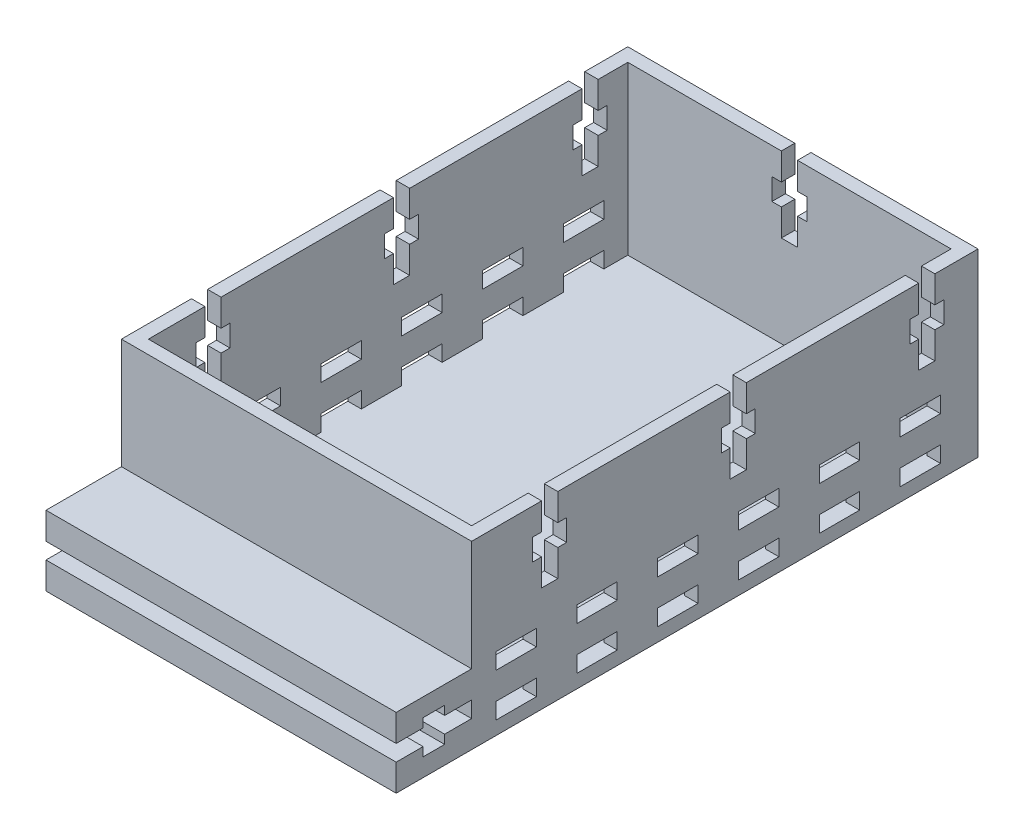
SolidWorks part; units mm, degrees
ref_plane "Front Plane" through (0, 0, 0) normal (0, 0, 1) x (1, 0, 0)
ref_plane "Top Plane" through (0, 0, 0) normal (0, 1, 0) x (1, 0, 0)
ref_plane "Right Plane" through (0, 0, 0) normal (1, 0, 0) x (0, 0, -1)
sketch "Sketch1" plane through (0, 0, 0) normal (0, 1, 0) x (1, 0, 0)
  line L1 (-30, 44.5) -> (30, 44.5)
  line L2 (-30, 44.5) -> (-30, -44.5)
  line L3 (-30, -44.5) -> (30, -44.5)
  line L4 (30, 44.5) -> (30, -44.5)
  point P4 (0, 44.5)
  point P6 (-30, 0)
  dimension "D1" = 89
  dimension "D2" = 60
extrude "Boss-Extrude1" add sketch "Sketch1" along normal blind 2.5
sketch "Sketch3" plane through (0, 0, 0) normal (0, 1, 0) x (1, 0, 0)
  line L0 (-30, 44.5) -> (-30, -44.5) construction
  line L1 (-32.5, 47) -> (32.5, 47)
  line L2 (-32.5, 47) -> (-32.5, -47)
  line L3 (-32.5, -47) -> (32.5, -47)
  line L4 (32.5, 47) -> (32.5, -47)
  line L5 (30, 44.5) -> (-30, 44.5) construction
  line L6 (30, -44.5) -> (30, 44.5) construction
  line L7 (-30, -44.5) -> (30, -44.5) construction
  line L9 (-30, 44.5) -> (30, 44.5)
  line L10 (-30, 44.5) -> (-30, -44.5)
  line L11 (-30, -44.5) -> (30, -44.5)
  line L12 (30, 44.5) -> (30, -44.5)
  dimension "D1" = 2.5
  dimension "D2" = 2.5
  dimension "D3" = 2.5
  dimension "D4" = 2.5
extrude "Boss-Extrude2" add sketch "Sketch3" along normal blind 33.5
sketch "Sketch5" plane through (0, 0, 0) normal (1, 0, 0) x (0, 0, -1)
  line L0 (-47, 0) -> (47, 0) construction
  line L1 (-42.4651, 2.5) -> (-34.9651, 2.5)
  line L2 (-42.4651, 2.5) -> (-42.4651, 5.5)
  line L3 (-42.4651, 5.5) -> (-34.9651, 5.5)
  line L4 (-34.9651, 2.5) -> (-34.9651, 5.5)
  dimension "D1" = 2.5
  dimension "D2" = 3
  dimension "D3" = 7.5
extrude "Cut-Extrude1" cut sketch "Sketch5" against normal through all both and the other way through all
pattern_linear "LPattern1" count 6 spacing 15 along (0, 0, -1) of "Cut-Extrude1"
pattern_linear "LPattern2" count 2 spacing 8 along (0, 1, 0) of "LPattern1", "Cut-Extrude1"
sketch "Sketch6" plane through (0, 0, 0) normal (0, 1, 0) x (1, 0, 0)
  line L0 (32.5, -47) -> (32.5, 47) construction
  line L1 (-32.5, -47) -> (32.5, -47)
  line L2 (-32.5, -47) -> (-32.5, -61)
  line L3 (-32.5, -61) -> (32.5, -61)
  line L4 (32.5, -47) -> (32.5, -61)
  dimension "D1" = 14
extrude "Boss-Extrude3" add sketch "Sketch6" along normal blind 13
sketch "Sketch7" plane through (0, 0, 0) normal (1, 0, 0) x (0, 0, -1)
  line L0 (-61, 8) -> (-56, 8)
  line L1 (-61, 13) -> (-61, 0) construction
  line L2 (-56, 8) -> (-56, 9.65)
  line L3 (-56, 9.65) -> (-52, 9.65)
  line L4 (-52, 9.65) -> (-52, 8)
  line L5 (-52, 8) -> (-47, 8)
  line L6 (-47, 8) -> (-47, 5)
  line L7 (-47, 5) -> (-52, 5)
  line L8 (-52, 5) -> (-52, 3.35)
  line L9 (-52, 3.35) -> (-56, 3.35)
  line L10 (-56, 3.35) -> (-56, 5)
  line L11 (-56, 5) -> (-61, 5)
  line L13 (-61, 8) -> (-61, 5)
  point P14 (-61, 6.5)
  point P15 (-61, 6.5)
  dimension "D1" = 5
  dimension "D2" = 4
  dimension "D3" = 3
  dimension "D4" = 1.65
  dimension "D5" = 1.65
  dimension "D6" = 5
extrude "Cut-Extrude2" cut sketch "Sketch7" against normal through all both and the other way through all
sketch "Sketch11" plane through (0, 0, 0) normal (1, 0, 0) x (0, 0, -1)
  line L12 (39, 33.5) -> (39, 28.5)
  line L13 (-47, 33.5) -> (47, 33.5) construction
  line L14 (39, 28.5) -> (40.65, 28.5)
  line L15 (40.65, 28.5) -> (40.65, 24.5)
  line L16 (40.65, 24.5) -> (39, 24.5)
  line L17 (39, 24.5) -> (39, 19.5)
  line L18 (39, 19.5) -> (36, 19.5)
  line L19 (36, 19.5) -> (36, 24.5)
  line L20 (36, 24.5) -> (34.35, 24.5)
  line L21 (34.35, 24.5) -> (34.35, 28.5)
  line L22 (34.35, 28.5) -> (36, 28.5)
  line L23 (36, 28.5) -> (36, 33.5)
  line L24 (36, 33.5) -> (39, 33.5)
  line L25 (47, 33.5) -> (47, 0) construction
  point P0 (37.5, 33.5)
  dimension "D7" = 5
  dimension "D8" = 4
  dimension "D9" = 1.65
  dimension "D10" = 1.65
  dimension "D11" = 5
  dimension "D12" = 3
  dimension "D2" = 9.5
extrude "Cut-Extrude3" cut sketch "Sketch11" against normal through all both and the other way through all
pattern_linear "LPattern3" count 3 spacing 35 along (0, 0, 1) of "Cut-Extrude3"
sketch "Sketch12" plane through (0, 0, 0) normal (0, 0, 1) x (1, 0, 0)
  line L0 (1.5, 33.5) -> (1.5, 28.5)
  line L1 (1.5, 28.5) -> (3.25, 28.5)
  line L2 (3.25, 28.5) -> (3.25, 24.5)
  line L3 (3.25, 24.5) -> (1.5, 24.5)
  line L4 (1.5, 24.5) -> (1.5, 19.5)
  line L5 (1.5, 19.5) -> (-1.5, 19.5)
  line L6 (-1.5, 19.5) -> (-1.5, 24.5)
  line L7 (-1.5, 24.5) -> (-3.25, 24.5)
  line L8 (-3.25, 24.5) -> (-3.25, 28.5)
  line L9 (-3.25, 28.5) -> (-1.5, 28.5)
  line L10 (-1.5, 28.5) -> (-1.5, 33.5)
  line L11 (-1.5, 33.5) -> (1.5, 33.5)
  line L12 (-32.5, 33.5) -> (32.5, 33.5) construction
  point P0 (0, 33.5)
  point P15 (0, 33.5)
  dimension "D1" = 5
  dimension "D2" = 4
  dimension "D3" = 1.75
  dimension "D4" = 1.75
  dimension "D5" = 5
  dimension "D6" = 3
extrude "Cut-Extrude4" cut sketch "Sketch12" against normal up to next
equation "\"wall\"=2.5"
equation "\"D1@Sketch3\"=\"wall\""
equation "\"D2@Sketch3\"=\"wall\""
equation "\"D3@Sketch3\"=\"wall\""
equation "\"D4@Sketch3\"=\"wall\""
equation "\"D1@Boss-Extrude2\"=\"wall\"+31"
equation "\"D1@Sketch5\"=\"wall\""
equation "\"prescrew\"=5"
equation "\"D1@Sketch7\"=\"prescrew\""
equation "\"nut\"=4"
equation "\"D2@Sketch7\"=\"nut\""
equation "\"nutextra\"=1.65"
equation "\"D5@Sketch7\"=\"nutextra\""
equation "\"D4@Sketch7\"=\"nutextra\""
equation "\"postscrew\"=5"
equation "\"D6@Sketch7\"=\"postscrew\""
equation "\"screw\"=3"
equation "\"D3@Sketch7\"=\"screw\""
equation "\"D7@Sketch11\"=\"prescrew\""
equation "\"D8@Sketch11\"=\"nut\""
equation "\"D9@Sketch11\"=\"nutextra\""
equation "\"D10@Sketch11\"=\"nutextra\""
equation "\"D11@Sketch11\"=\"postscrew\""
equation "\"D12@Sketch11\"=\"screw\""
equation "\"D2@Sketch11\"=\"wall\"+7"
